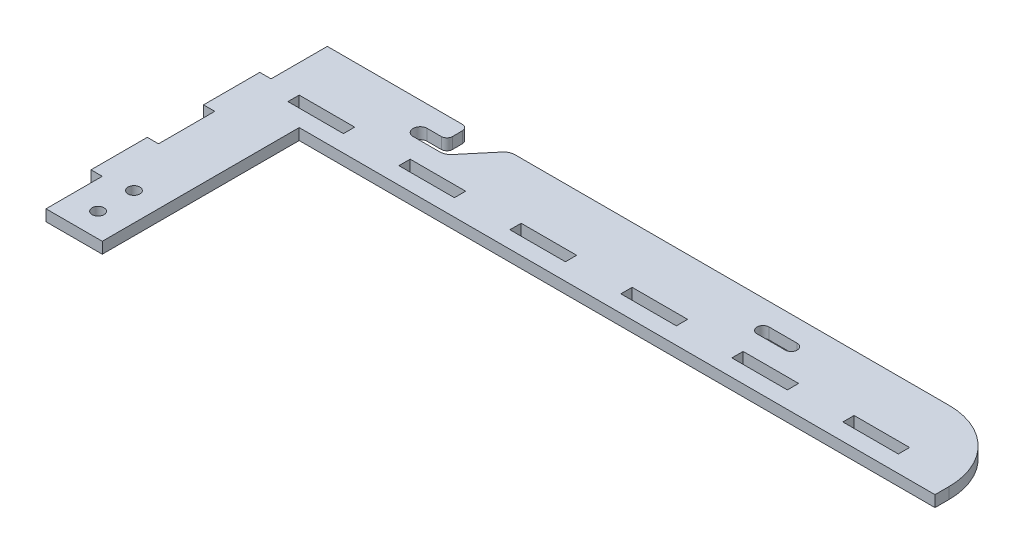
SolidWorks part; units mm, degrees
ref_plane "Front Plane" through (0, 0, 0) normal (0, 0, 1) x (1, 0, 0)
ref_plane "Top Plane" through (0, 0, 0) normal (0, 1, 0) x (1, 0, 0)
ref_plane "Right Plane" through (0, 0, 0) normal (1, 0, 0) x (0, 0, -1)
sketch "Sketch1" plane through (0, 0, 0) normal (0, 1, 0) x (1, 0, 0)
  line L0 (0, -24.6267) -> (0, 100.5806) construction
  line L1 (4, 0) -> (4, 20)
  line L2 (4, 20) -> (0, 20)
  line L3 (0, 20) -> (0, 40)
  line L4 (0, 40) -> (4, 40)
  line L5 (4, 40) -> (4, 60)
  line L6 (4, 60) -> (0, 60)
  line L7 (0, 60) -> (0, 80)
  line L8 (0, 80) -> (4, 80)
  line L9 (4, 80) -> (4, 100)
  line L10 (0, 0) -> (4, 0) construction
  line L11 (4, 0) -> (24, 0)
  line L12 (24, 0) -> (24, 70)
  line L13 (24, 70) -> (250, 70)
  line L15 (225, 100) -> (70.6793, 100)
  line L16 (251.0496, 76) -> (-35.0505, 76) construction
  line L17 (14, 0) -> (14, 49.3314) construction
  line L18 (53.45, 76) -> (53.45, 80)
  line L19 (14, 76) -> (33.725, 76)
  line L20 (14, 76) -> (14, 80)
  line L21 (14, 80) -> (33.725, 80)
  line L22 (33.725, 76) -> (33.725, 80)
  line L23 (53.45, 76) -> (73.175, 76)
  line L24 (73.175, 76) -> (73.175, 80)
  line L25 (53.45, 80) -> (73.175, 80)
  line L26 (92.9, 76) -> (92.9, 80)
  line L27 (92.9, 76) -> (112.625, 76)
  line L28 (112.625, 76) -> (112.625, 80)
  line L29 (92.9, 80) -> (112.625, 80)
  line L30 (132.35, 76) -> (132.35, 80)
  line L31 (132.35, 76) -> (152.075, 76)
  line L32 (152.075, 76) -> (152.075, 80)
  line L33 (132.35, 80) -> (152.075, 80)
  line L34 (171.8, 76) -> (171.8, 80)
  line L35 (171.8, 76) -> (191.525, 76)
  line L36 (191.525, 76) -> (191.525, 80)
  line L37 (171.8, 80) -> (191.525, 80)
  line L38 (211.25, 76) -> (211.25, 80)
  line L39 (211.25, 76) -> (230.975, 76)
  line L40 (230.975, 76) -> (230.975, 80)
  line L41 (211.25, 80) -> (230.975, 80)
  line L42 (288.5555, 90) -> (206.8646, 90) construction
  line L43 (168.885, 90) -> (178.885, 90) construction
  line L44 (168.885, 92.125) -> (178.885, 92.125)
  line L45 (168.885, 87.875) -> (178.885, 87.875)
  line L46 (54, 98) -> (54, 94.5)
  line L47 (52, 92.5) -> (47, 92.5)
  line L48 (47, 87.5) -> (56.4601, 87.5)
  line L49 (59.5243, 88.9288) -> (67.6151, 98.5712)
  line L50 (52, 100) -> (4, 100)
  line L51 (250, 70) -> (250, 75)
  circle A0 centre (14, 8.5) radius 2.125
  circle A1 centre (14, 21.25) radius 2.125
  arc A2 (168.885, 92.125) -> (168.885, 87.875) centre (168.885, 90) ccw
  arc A3 (178.885, 87.875) -> (178.885, 92.125) centre (178.885, 90) ccw
  arc A5 (47, 92.5) -> (47, 87.5) centre (47, 90) ccw
  arc A6 (56.4601, 87.5) -> (59.5243, 88.9288) centre (56.4601, 91.5) ccw
  arc A7 (67.6151, 98.5712) -> (70.6793, 100) centre (70.6793, 96) cw
  arc A8 (54, 98) -> (52, 100) centre (52, 98) ccw
  arc A9 (54, 94.5) -> (52, 92.5) centre (52, 94.5) cw
  arc A10 (250, 75) -> (225, 100) centre (225, 75) ccw
  point P54 (173.885, 90)
  point P61 (250, 100)
  point P75 (54, 100)
  point P79 (250, 100)
  dimension "D8" = 4.25
  dimension "D14" = 2.125
  dimension "D17" = 76.115
  dimension "D19" = 4
  dimension "D20" = 4
  dimension "D21" = 2
  dimension "D22" = 2
  dimension "D23" = 2.5
  dimension "D15" = 25
  dimension "D1" = 20
  dimension "D2" = 100
  dimension "D3" = 4
  dimension "D4" = 20
  dimension "D5" = 246
  dimension "D6" = 30
  dimension "D7" = 6
  dimension "D9" = 8.5
  dimension "D10" = 12.75
  dimension "D11" = 10
  dimension "D12" = 19.725
  dimension "D13" = 4
  dimension "D16" = 10
  dimension "D24" = 7.5
  dimension "D25" = 130
  dimension "D26" = 50
  dimension "D27" = 5
  dimension "D28" = 10
  dimension "D18" = 6
extrude "Boss-Extrude1" add sketch "Sketch1" along normal blind 4
